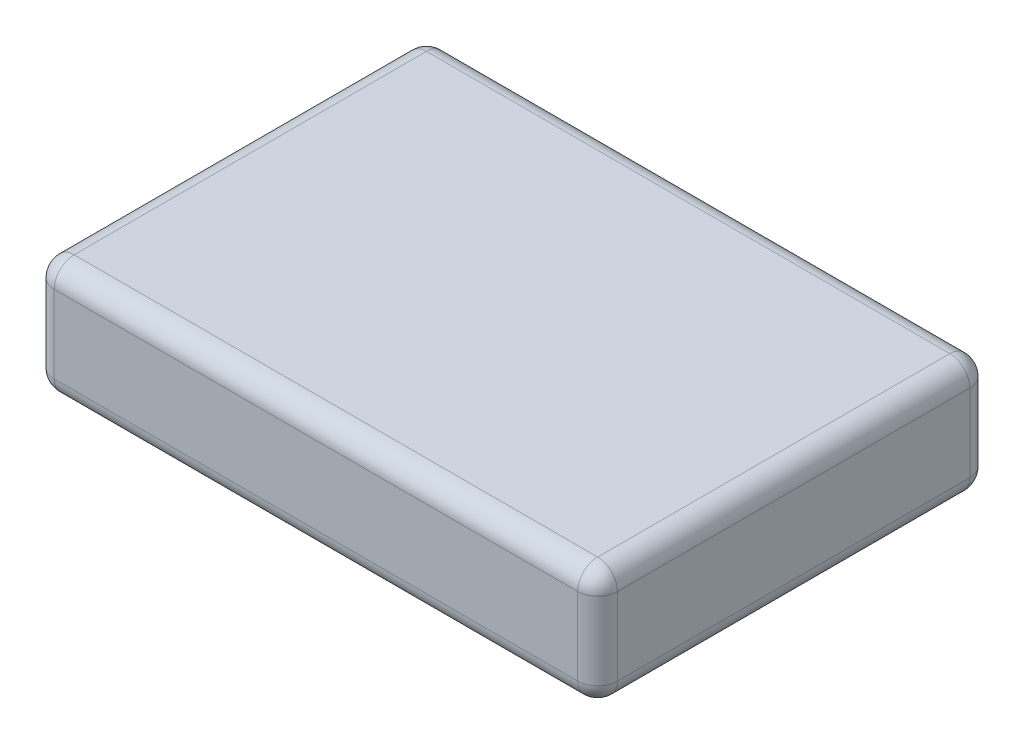
SolidWorks part; units mm, degrees
ref_plane "Front Plane" through (0, 0, 0) normal (0, 0, 1) x (1, 0, 0)
ref_plane "Top Plane" through (0, 0, 0) normal (0, 1, 0) x (1, 0, 0)
ref_plane "Right Plane" through (0, 0, 0) normal (1, 0, 0) x (0, 0, -1)
sketch "Sketch1" plane through (0, 0, 0) normal (0, 1, 0) x (1, 0, 0)
  line L1 (35.941, 25.019) -> (-35.941, 25.019)
  line L2 (35.941, 25.019) -> (35.941, -25.019)
  line L3 (35.941, -25.019) -> (-35.941, -25.019)
  line L4 (-35.941, 25.019) -> (-35.941, -25.019)
  line L5 (35.941, 25.019) -> (-35.941, -25.019) construction
  line L6 (35.941, -25.019) -> (-35.941, 25.019) construction
  point P0 (0, 0)
  dimension "D1" = 71.882
  dimension "D2" = 50.038
extrude "Boss-Extrude1" add sketch "Sketch1" along normal blind 14.986
fillet "Fillet1" radius 2.54 12 edges at (-35.941, 7.493, 25.019) (35.941, 7.493, 25.019) (35.941, 7.493, -25.019) (-35.941, 7.493, -25.019) (0, 14.986, -25.019) (35.941, 14.986, 0) (0, 14.986, 25.019) (-35.941, 14.986, 0) (0, 0, -25.019) (35.941, 0, 0) (0, 0, 25.019) (-35.941, 0, 0)
